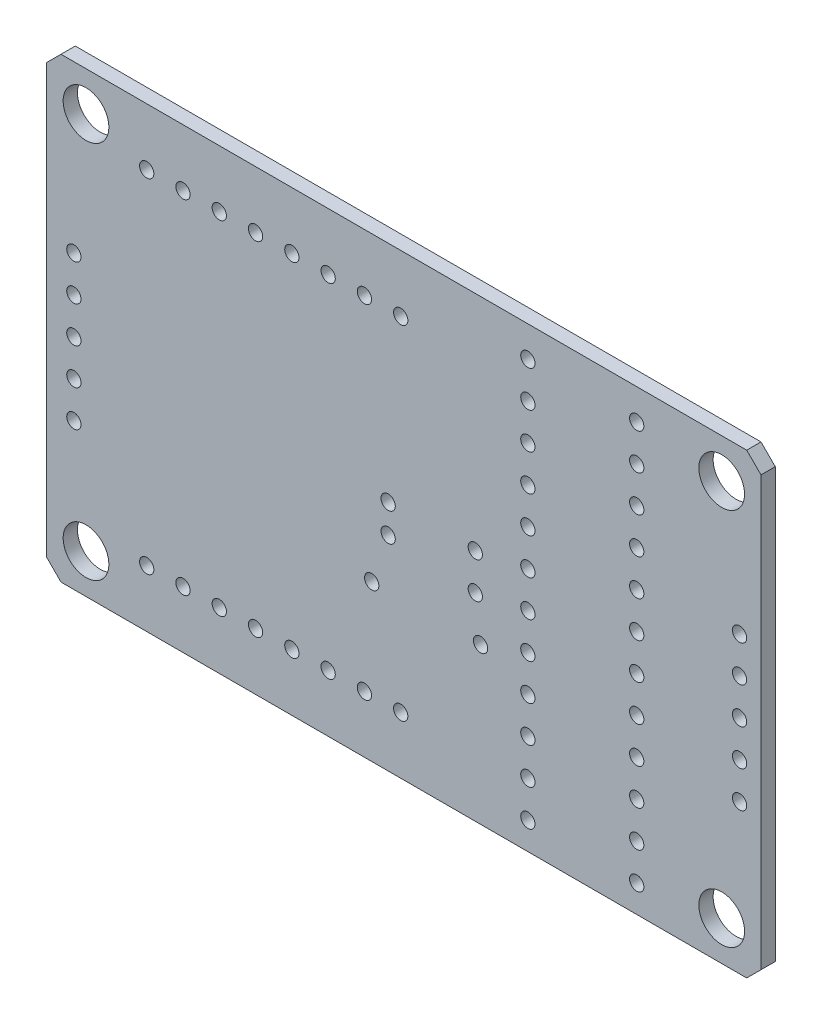
SolidWorks part; units mm, degrees
ref_plane "Front Plane" through (0, 0, 0) normal (0, 0, 1) x (1, 0, 0)
ref_plane "Top Plane" through (0, 0, 0) normal (0, 1, 0) x (1, 0, 0)
ref_plane "Right Plane" through (0, 0, 0) normal (1, 0, 0) x (0, 0, -1)
sketch "Sketch1" plane through (0, 0, 0) normal (0, 0, 1) x (1, 0, 0)
  line L0 (-28.3747, 11.4715) -> (31.6253, 11.4715) construction
  line L1 (-22.25, 13.25) -> (-22.25, -13.25) construction
  line L2 (25, -16) -> (-25, -16)
  line L3 (25, -16) -> (25, 16)
  line L4 (25, 16) -> (-25, 16)
  line L5 (-25, -16) -> (-25, 16)
  line L6 (25, -16) -> (-25, 16) construction
  line L7 (25, 16) -> (-25, -16) construction
  line L8 (-22.25, -13.25) -> (22.25, -13.25) construction
  line L9 (22.25, -13.25) -> (22.25, 13.25) construction
  line L10 (22.25, 13.25) -> (-22.25, 13.25) construction
  line L11 (-22.25, 0) -> (0, 0) construction
  line L12 (0, 0) -> (22.25, 0) construction
  circle A0 centre (-22.25, -13.25) radius 1.6
  circle A1 centre (22.25, -13.25) radius 1.6
  circle A2 centre (22.25, 13.25) radius 1.6
  circle A3 centre (-22.25, 13.25) radius 1.6
  point P2 (0, 0)
  dimension "D5" = 3.2
  dimension "D1" = 60
  dimension "D2" = 50
  dimension "D3" = 32
  dimension "D4" = 44.5
  dimension "D6" = 26.5
extrude "Boss-Extrude1" add sketch "Sketch1" along normal blind 1
sketch "Sketch3" plane through (0, 0, 0) normal (0, 0, -1) x (-1, 0, 0)
  line L0 (-24.8567, 0.1327) -> (25.1427, 0.3778) construction
  line L1 (25, 16) -> (25, -16) construction
  line L2 (-25, -16) -> (-25, 16) construction
  line L3 (-25, 16) -> (25, 16) construction
  circle A11 centre (-23.5, 4.6) radius 0.5
  circle A12 centre (-23.5, 2.06) radius 0.5
  circle A13 centre (-23.5, -0.48) radius 0.5
  circle A14 centre (-23.5, -3.02) radius 0.5
  circle A15 centre (-23.5, -5.56) radius 0.5
  circle A16 centre (-16.3, 13.85) radius 0.5
  circle A17 centre (-16.3, 11.31) radius 0.5
  circle A18 centre (-16.3, 8.77) radius 0.5
  circle A19 centre (-16.3, 6.23) radius 0.5
  circle A20 centre (-16.3, 3.69) radius 0.5
  circle A21 centre (-16.3, 1.15) radius 0.5
  circle A22 centre (-16.3, -1.39) radius 0.5
  circle A23 centre (-16.3, -3.93) radius 0.5
  circle A24 centre (-16.3, -6.47) radius 0.5
  circle A25 centre (-16.3, -9.01) radius 0.5
  circle A26 centre (-16.3, -11.55) radius 0.5
  circle A27 centre (-16.3, -14.09) radius 0.5
  circle A28 centre (-8.68, 13.85) radius 0.5
  circle A29 centre (-8.68, 11.31) radius 0.5
  circle A30 centre (-8.68, 8.77) radius 0.5
  circle A31 centre (-8.68, 6.23) radius 0.5
  circle A32 centre (-8.68, 3.69) radius 0.5
  circle A33 centre (-8.68, 1.15) radius 0.5
  circle A34 centre (-8.68, -1.39) radius 0.5
  circle A35 centre (-8.68, -3.93) radius 0.5
  circle A36 centre (-8.68, -6.47) radius 0.5
  circle A37 centre (-8.68, -9.01) radius 0.5
  circle A38 centre (-8.68, -11.55) radius 0.5
  circle A39 centre (-8.68, -14.09) radius 0.5
  circle A40 centre (18, 12) radius 0.5
  circle A41 centre (15.46, 12) radius 0.5
  circle A42 centre (12.92, 12) radius 0.5
  circle A43 centre (10.38, 12) radius 0.5
  circle A44 centre (7.84, 12) radius 0.5
  circle A45 centre (5.3, 12) radius 0.5
  circle A46 centre (2.76, 12) radius 0.5
  circle A47 centre (0.22, 12) radius 0.5
  circle A48 centre (18, -12) radius 0.5
  circle A49 centre (15.46, -12) radius 0.5
  circle A50 centre (12.92, -12) radius 0.5
  circle A51 centre (10.38, -12) radius 0.5
  circle A52 centre (7.84, -12) radius 0.5
  circle A53 centre (5.3, -12) radius 0.5
  circle A54 centre (2.76, -12) radius 0.5
  circle A55 centre (0.22, -12) radius 0.5
  circle A56 centre (23.1, 4.4) radius 0.5
  circle A57 centre (23.1, 1.86) radius 0.5
  circle A58 centre (23.1, -0.68) radius 0.5
  circle A59 centre (23.1, -3.22) radius 0.5
  circle A60 centre (23.1, -5.76) radius 0.5
  circle A61 centre (-5, 0.4) radius 0.5
  circle A62 centre (-5, -2.14) radius 0.5
  circle A63 centre (-5.37, -5.1) radius 0.5
  circle A64 centre (2.25, -5.1) radius 0.5
  circle A65 centre (1.1, 0.3) radius 0.5
  circle A66 centre (1.1, -1.7) radius 0.5
  dimension "D1" = 1
  dimension "D5" = 1
  dimension "D11" = 1
  dimension "D25" = 1
  dimension "D3" = 1.5
  dimension "D4" = 11.4
  dimension "D7" = 2.15
  dimension "D8" = 8.7
  dimension "D9" = 7.62
  dimension "D13" = 7
  dimension "D14" = 4
  dimension "D16" = 24
  dimension "D17" = 11.6
  dimension "D18" = 1.9
  dimension "D20" = 2.54
  dimension "D21" = 2
  dimension "D22" = 7.62
  dimension "D23" = 1.1
  dimension "D24" = 0.3
  dimension "D26" = 5
  dimension "D27" = 0.4
  dimension "D28" = 5.1
  dimension "D29" = 2.25
  dimension "D2" = 5
  dimension "D6" = 12
  dimension "D10" = 12
  dimension "D12" = 8
  dimension "D15" = 8
  dimension "D19" = 5
extrude "Cut-Extrude1" cut sketch "Sketch3" against normal up to surface (1 mm away) up to face at (23.85, 13.25, 1)
chamfer "Chamfer1" distance 1 angle 45 4 edges at (-25, 16, 0.5) (-25, -16, 0.5) (25, 16, 0.5) (25, -16, 0.5)
